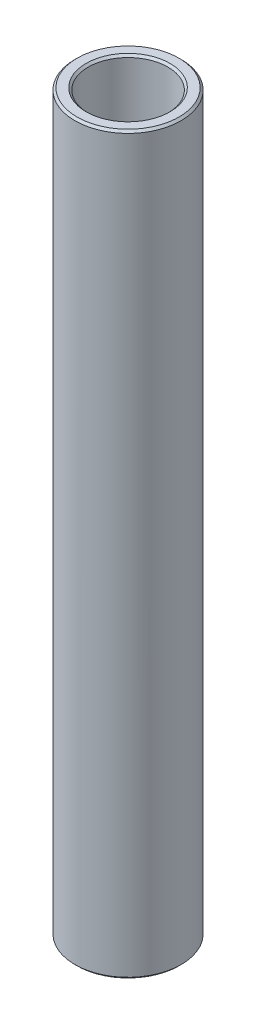
SolidWorks part; units mm, degrees
ref_plane "Front Plane" through (0, 0, 0) normal (0, 0, 1) x (1, 0, 0)
ref_plane "Top Plane" through (0, 0, 0) normal (0, 1, 0) x (1, 0, 0)
ref_plane "Right Plane" through (0, 0, 0) normal (1, 0, 0) x (0, 0, -1)
sketch "Sketch1" plane through (0, 0, 0) normal (0, 0, 1) x (1, 0, 0)
  line L0 (4.7625, 70.6437) -> (4.7625, 158.5087)
  line L1 (4.7625, 158.5087) -> (6.35, 158.5087)
  line L2 (6.35, 158.5087) -> (6.35, 70.6437)
  line L3 (6.35, 70.6437) -> (4.7625, 70.6437)
  line L4 (-10.0875, 79.3749) -> (-120.0875, 79.3749) construction
  line L6 (0, 61.1187) -> (0, 168.0337) construction
  dimension "D1" = 9.525
  dimension "D2" = 9.525
  dimension "D3" = 12.7
  dimension "D4" = 9.525
revolve "Revolve1" add sketch "Sketch1" angle 360 about L6
chamfer "Chamfer1" distance 0.254 angle 45 4 edges at (6.35, 158.5087, 0) (4.7625, 158.5087, 0) (4.7625, 70.6437, 0) (6.35, 70.6437, 0)
equation "\"D4@Sketch1\"=\"D1@Sketch1\""
